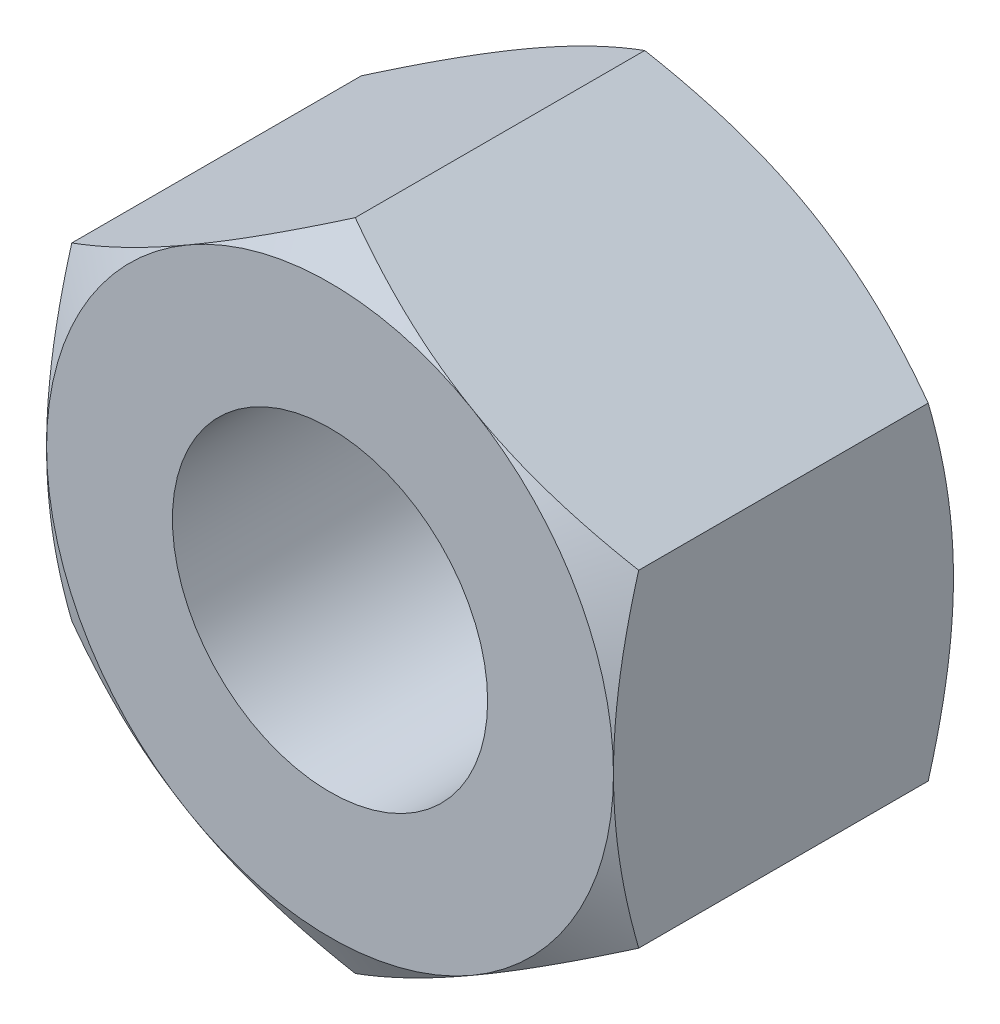
SolidWorks part; units mm, degrees
extrude "BaseNut" add sketch "BaseNutSke" against normal blind 8.5598
sketch "BaseNutSke" plane through (0, 0, 0) normal (0, 0, 1) x (1, 0, 0)
  line L6 (7.1374, 4.1208) -> (7.1374, -4.1208)
  line L7 (-7.1374, 4.1208) -> (-7.1374, -4.1208)
  line L8 (7.1374, 4.1208) -> (0, 8.2416)
  line L9 (0, 8.2416) -> (-7.1374, 4.1208)
  line L10 (-7.1374, -4.1208) -> (0, -8.2416)
  line L11 (0, -8.2416) -> (7.1374, -4.1208)
  circle A0 centre (0, 0) radius 3.9688
  dimension "Tap_drill" = 7.9375
  dimension "Width_flats" = 14.2748
  dimension "D2" = 7.1374
  dimension "D3" = 7.1374
  dimension "D1" = 120
  dimension "D4" = 7.1374
pattern_linear "ThdSchPat" [suppressed]
revolve "ThreadSchematic" [suppressed] cut sketch "ThdSchSke" angle 360 about L6
sketch "ThdSchSke" plane through (0, 0, 0) normal (0, 1, 0) x (1, 0, 0)
  line L0 (-3.175, 0.0254) -> (-3.9688, -0.5304)
  line L1 (-3.9688, -0.5304) -> (-1.9844, -0.5304)
  line L2 (-1.9844, -0.5304) -> (-1.9844, 0.5812)
  line L3 (-1.9844, 0.5812) -> (-3.9688, 0.5812)
  line L4 (-3.9688, 0.5812) -> (-3.175, 0.0254)
  line L5 (-3.175, 1.5875) -> (3.175, 1.5875) construction
  line L6 (0, 1.5875) -> (0, -2.9874) construction
  line L7 (0, 8.5598) -> (0, 0) construction
  dimension "SideAngle" = 55
  dimension "Advance" = 1.5875
  dimension "D1" = 0.0254
ref_plane "Plane1" through (0, 0, 0) normal (0, 0, 1) x (1, 0, 0)
ref_plane "Plane2" through (0, 0, 0) normal (0, 1, 0) x (1, 0, 0)
ref_plane "Plane3" through (0, 0, 0) normal (1, 0, 0) x (0, 0, -1)
sketch "Sketch4" plane through (0, 0, 0) normal (1, 0, 0) x (0, 0, -1)
  line L0 (8.5598, 7.1374) -> (8.1534, 7.1374)
  line L1 (8.5598, 7.1374) -> (8.5598, 20.9416)
  line L2 (8.1534, 20.9416) -> (8.5598, 20.9416)
  line L3 (8.1534, 20.9416) -> (8.1534, 7.1374)
  line L4 (0, 0) -> (34.925, 0) construction
  line L6 (8.5598, 4.1208) -> (8.5598, 8.2416) construction
  line L7 (0, 7.1374) -> (-12.7, 7.1374)
  line L8 (0, 4.1208) -> (0, 8.2416) construction
  line L9 (0.635, 8.2416) -> (0.635, 20.9416)
  line L10 (0.635, 20.9416) -> (-12.7, 20.9416)
  line L11 (-12.7, 20.9416) -> (-12.7, 7.1374)
  line L12 (0, 7.1374) -> (0.635, 8.2416)
  line L14 (0, 4.1208) -> (0, -4.1208) construction
  line L15 (8.5598, 8.2416) -> (0, 8.2416) construction
  dimension "D1" = 7.1374
  dimension "D2" = 0.635
  dimension "D3" = 12.7
  dimension "D4" = 12.7
revolve "Bearing-Face" [suppressed] cut sketch "Sketch4" angle 360 about L4
sketch "Sketch3" plane through (0, 0, 0) normal (1, 0, 0) x (0, 0, -1)
  line L0 (8.5598, 7.1374) -> (7.9248, 8.2416)
  line L1 (7.9248, 8.2416) -> (7.9248, 20.9416)
  line L2 (7.9248, 20.9416) -> (21.2598, 20.9416)
  line L3 (21.2598, 20.9416) -> (21.2598, 7.1374)
  line L4 (21.2598, 7.1374) -> (8.5598, 7.1374)
  line L5 (8.5598, 4.1208) -> (8.5598, 8.2416) construction
  line L6 (8.5598, 8.2416) -> (0, 8.2416) construction
  line L7 (0, 0) -> (38.6776, 0) construction
  line L8 (8.5598, 0) -> (0, 0) construction
  line L9 (4.2799, 8.2416) -> (4.2799, 44.222) construction
  line L10 (0.635, 20.9416) -> (-12.7, 20.9416)
  line L11 (-12.7, 20.9416) -> (-12.7, 7.1374)
  line L12 (-12.7, 7.1374) -> (0, 7.1374)
  line L13 (0, 7.1374) -> (0.635, 8.2416)
  line L14 (0.635, 8.2416) -> (0.635, 20.9416)
  line L16 (8.5598, 8.2416) -> (0, 8.2416) construction
  dimension "D1" = 7.1374
  dimension "D2" = 0.635
  dimension "D4" = 12.7
  dimension "D3" = 12.7
revolve "Double-Chamfer" cut sketch "Sketch3" angle 360 about L7
sketch "Sketch5" plane through (0, 0, 0) normal (1, 0, 0) x (0, 0, -1)
  line L0 (8.5344, 3.175) -> (8.0551, 2.4905)
  line L1 (8.5852, 3.175) -> (8.5344, 3.175)
  line L2 (8.5852, 3.175) -> (8.5852, 2.4905)
  line L3 (8.5852, 2.4905) -> (8.0551, 2.4905)
  line L6 (-0.0508, 3.175) -> (0, 3.175)
  line L7 (0, 3.175) -> (0.4793, 2.4905)
  line L9 (0.4793, 2.4905) -> (-0.0508, 2.4905)
  line L10 (-0.0508, 2.4905) -> (-0.0508, 3.175)
  line L11 (25.0375, 0) -> (38.388, 0) construction
  line L12 (8.5598, 0) -> (0, 0) construction
  dimension "D1" = 35
  dimension "D2" = 0.0508
  dimension "ThreadMajor" = 3.175
  dimension "Offset1" = 8.5852
revolve "EndChamfer" cut sketch "Sketch5" angle 360 about L11
equation "\"D2@BaseNutSke\" = \"Width_flats@BaseNutSke\" / 2"
equation "\"D3@BaseNutSke\" = \"Width_flats@BaseNutSke\" / 2"
equation "\"D1@Sketch3\" = \"Width_flats@BaseNutSke\" /2"
equation "\"D1@Sketch4\" = \"D2@BaseNutSke\""
equation "\"D4@BaseNutSke\" = \"D3@BaseNutSke\""
equation "\"Tap_Drill@ThdSchSke\" = \"Tap_drill@BaseNutSke\""
equation "\"OverCut@ThdSchSke\" = \"Tap_Drill@ThdSchSke\" * 0.5"
equation "\"Num_threads@ThdSchPat\" = int(  ( \"Thickness@BaseNut\" - 0.002 ) / \"Advance@ThdSchSke\" + 0.999 )  + 1"
equation "\"Advance@ThdSchPat\" = ( \"Thickness@BaseNut\" - 0.002 ) /  (\"Num_threads@ThdSchPat\" - 1) 'relax it"
equation "' \"Num_threads@ThdSchPat\" = \"Num_threads@ThdSchPat\" - sgn( \"Num_threads@ThdSchPat\" - 1) '---chamfered tips only---"
equation "\"Offset1@Sketch5\" = \"Thickness@BaseNut\" + 0.001"
equation "\"Offset2@Sketch5\" = \"Offset1@Sketch5\" + 0.002"
